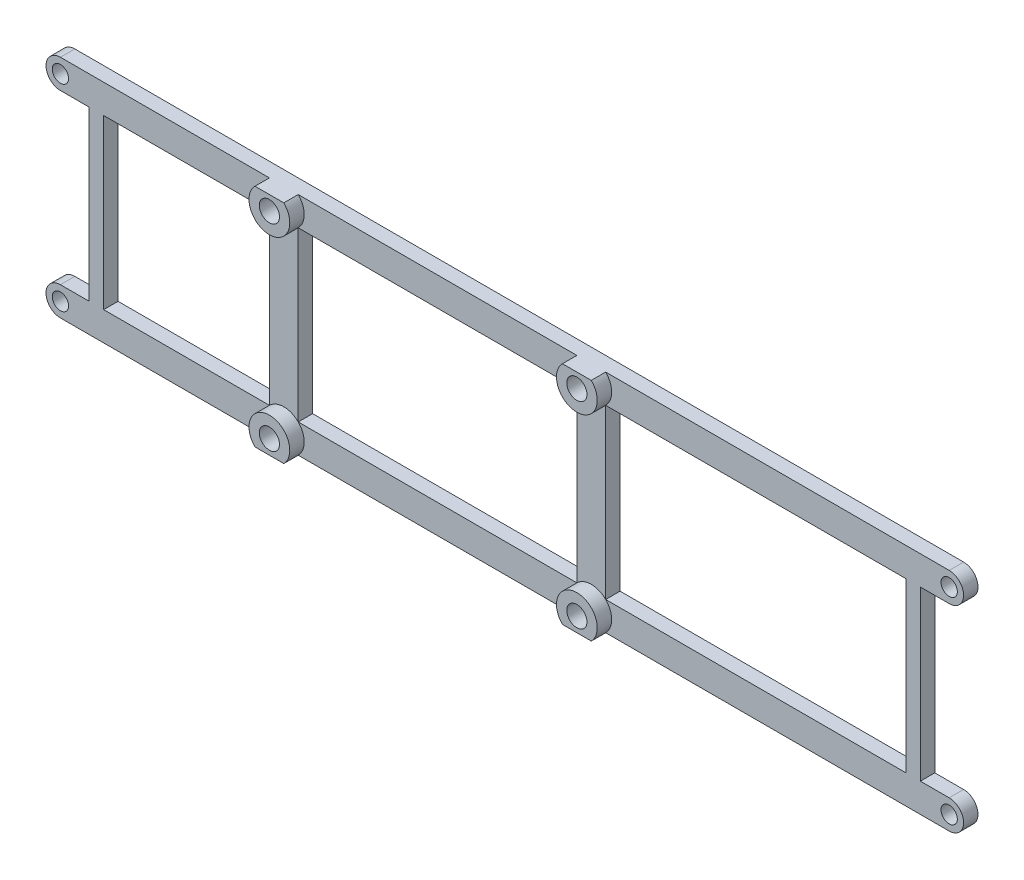
SolidWorks part; units mm, degrees
ref_plane "Plano frontal" through (0, 0, 0) normal (0, 0, 1) x (1, 0, 0)
ref_plane "Plano superior" through (0, 0, 0) normal (0, 1, 0) x (1, 0, 0)
ref_plane "Plano direito" through (0, 0, 0) normal (1, 0, 0) x (0, 0, -1)
sketch "Esboço1" plane through (0, 0, 0) normal (0, 0, 1) x (1, 0, 0)
  line L0 (92.5, 23.5) -> (-92.5, 23.5)
  line L1 (-92.5, 17.5) -> (-49, 17.5)
  line L2 (-49, 17.5) -> (-49, -17.5)
  line L3 (-12.3464, 0) -> (0, 0) construction
  line L4 (0, -13.606) -> (0, 13.606) construction
  line L5 (92.5, 17.5) -> (21, 17.5)
  line L6 (21, 17.5) -> (21, -17.5)
  line L7 (-43, -17.5) -> (-43, 17.5)
  line L8 (-43, 17.5) -> (15, 17.5)
  line L9 (15, 17.5) -> (15, -17.5)
  line L10 (-49, 17.5) -> (-43, 17.5) construction
  line L11 (15, 17.5) -> (21, 17.5) construction
  line L12 (21, 23.5) -> (21, 17.5) construction
  line L13 (21, -23.5) -> (21, -17.5) construction
  line L14 (15, -17.5) -> (21, -17.5) construction
  line L15 (-49, -17.5) -> (-43, -17.5) construction
  line L16 (-43, -17.5) -> (15, -17.5)
  line L17 (92.5, -17.5) -> (21, -17.5)
  line L18 (-92.5, -17.5) -> (-49, -17.5)
  line L19 (92.5, -23.5) -> (-92.5, -23.5)
  arc A0 (-92.5, 23.5) -> (-92.5, 17.5) centre (-92.5, 20.5) ccw
  arc A1 (92.5, 23.5) -> (92.5, 17.5) centre (92.5, 20.5) cw
  circle A2 centre (-92.5, 20.5) radius 1.7
  circle A3 centre (92.5, 20.5) radius 1.7
  circle A4 centre (18, 20.5) radius 1.7
  circle A5 centre (-46, 20.5) radius 1.7
  circle A6 centre (-46, -20.5) radius 1.7
  circle A7 centre (18, -20.5) radius 1.7
  circle A8 centre (92.5, -20.5) radius 1.7
  circle A9 centre (-92.5, -20.5) radius 1.7
  arc A10 (92.5, -23.5) -> (92.5, -17.5) centre (92.5, -20.5) ccw
  arc A11 (-92.5, -23.5) -> (-92.5, -17.5) centre (-92.5, -20.5) cw
  point P13 (21, 0)
  point P14 (-49, 0)
  point P18 (-43, 0)
  point P25 (0, 0)
  point P26 (-46, 17.5)
  point P27 (18, 17.5)
  point P28 (-6.2761, 26.4023)
  point P47 (15, 0)
  dimension "D1" = 3.4
  dimension "D2" = 3
  dimension "D3" = 185
  dimension "D4" = 64
  dimension "D5" = 41
  dimension "D6" = 43.5
extrude "Ressalto-extrusão1" add sketch "Esboço1" along normal blind 3
sketch "Esboço2" plane through (0, 0, 3) normal (0, 0, 1) x (1, 0, 0)
  line L0 (92.5, 23.5) -> (-92.5, 23.5) construction
  line L1 (-92.5, -23.5) -> (92.5, -23.5) construction
  line L2 (21, 23.5) -> (15, 23.5)
  line L3 (-49, -23.5) -> (-43, -23.5)
  line L4 (-43, 23.5) -> (-49, 23.5)
  line L5 (15, -23.5) -> (21, -23.5)
  arc A0 (-49, 23.5) -> (-43, 23.5) centre (-46, 20.5) ccw
  arc A1 (15, 23.5) -> (21, 23.5) centre (18, 20.5) ccw
  arc A2 (21, -23.5) -> (15, -23.5) centre (18, -20.5) ccw
  arc A3 (-43, -23.5) -> (-49, -23.5) centre (-46, -20.5) ccw
  circle A8 centre (-46, -20.5) radius 2.1
  circle A9 centre (18, -20.5) radius 2.1
  circle A10 centre (18, 20.5) radius 2.1
  circle A11 centre (-46, 20.5) radius 2.1
  point P1 (0, 0)
  dimension "D1" = 4.2
extrude "Ressalto-extrusão2" add sketch "Esboço2" along normal blind 3
sketch "Esboço3" plane through (0, 0, 3) normal (0, 0, 1) x (1, 0, 0)
  line L0 (-85, 17.5) -> (-85, -17.5)
  line L3 (-92.5, 17.5) -> (-49, 17.5) construction
  line L4 (-49, -17.5) -> (-92.5, -17.5) construction
  line L6 (21, 17.5) -> (92.5, 17.5) construction
  line L7 (85, 17.5) -> (85, -17.5)
  line L8 (92.5, -17.5) -> (21, -17.5) construction
  circle A0 centre (92.5, 20.5) radius 1.7 construction
  circle A1 centre (-92.5, 20.5) radius 1.7 construction
  dimension "D1" = 7.5
  dimension "D2" = 7.5
extrude "Extrusão-Fina1" add sketch "Esboço3" against normal through all thin thin type mid plane wall 3
